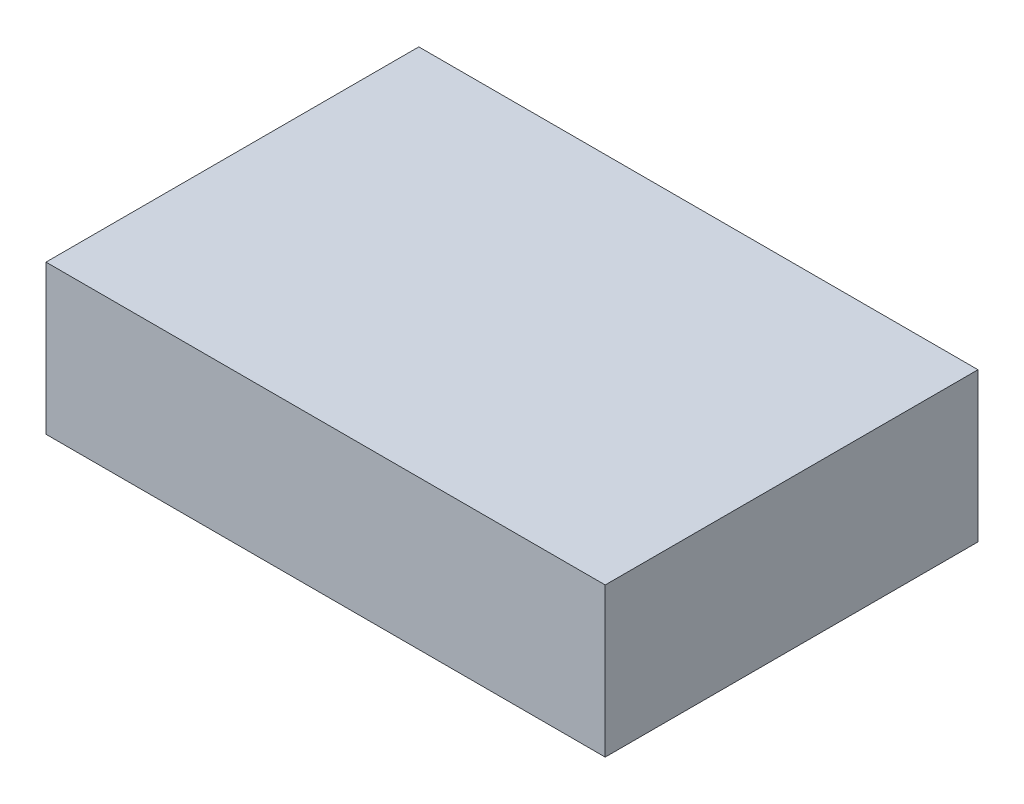
SolidWorks part; units mm, degrees
ref_plane "Front Plane" through (0, 0, 0) normal (0, 0, 1) x (1, 0, 0)
ref_plane "Top Plane" through (0, 0, 0) normal (0, 1, 0) x (1, 0, 0)
ref_plane "Right Plane" through (0, 0, 0) normal (1, 0, 0) x (0, 0, -1)
sketch "Sketch1" plane through (0, 0, 0) normal (0, 1, 0) x (1, 0, 0)
  line L1 (-102.8422, 49.4924) -> (47.1578, 49.4924)
  line L2 (-102.8422, 49.4924) -> (-102.8422, -50.5076)
  line L3 (-102.8422, -50.5076) -> (47.1578, -50.5076)
  line L4 (47.1578, 49.4924) -> (47.1578, -50.5076)
  dimension "D1" = 100
  dimension "D2" = 150
extrude "Boss-Extrude1" add sketch "Sketch1" along normal blind 40 contours L3 L4 L1 L2
